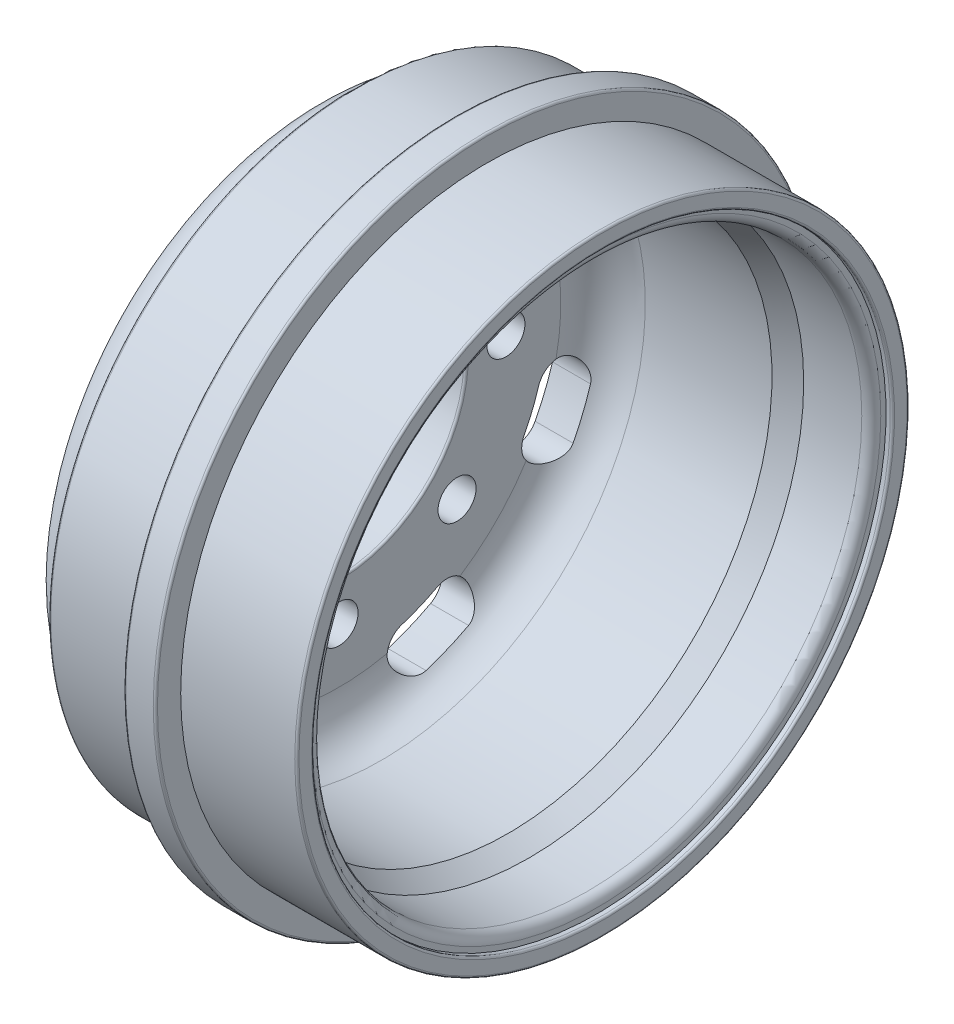
SolidWorks part; units mm, degrees
ref_plane "Plan de face" through (0, 0, 0) normal (0, 0, 1) x (1, 0, 0)
ref_plane "Plan de dessus" through (0, 0, 0) normal (0, 1, 0) x (1, 0, 0)
ref_plane "Plan de droite" through (0, 0, 0) normal (1, 0, 0) x (0, 0, -1)
sketch "Esquisse1" plane through (0, 0, 0) normal (0, 0, 1) x (1, 0, 0)
  line L0 (0, 0) -> (29.5727, 0) construction
  line L1 (0, 6.025) -> (1.75, 6.025)
  line L2 (1.75, 10.5) -> (1.75, 6.025)
  line L3 (14.25, 14.5) -> (8.75, 14.5)
  line L4 (8.75, 14.5) -> (8.75, 15.7)
  line L5 (8.75, 15.7) -> (7.25, 15.7)
  line L6 (7.25, 15.7) -> (7.25, 14.5)
  line L7 (7.25, 14.5) -> (2.5, 14.5)
  line L8 (2.5, 14.5) -> (2.5, 13.5)
  line L9 (0, 6.025) -> (0, 9.75)
  line L10 (0, 9.75) -> (0.5, 9.75)
  line L11 (0.5, 9.75) -> (0.5, 12)
  line L12 (14.25, 14.5) -> (14.25, 13.7)
  line L13 (14.25, 13.7) -> (13.95, 13.7)
  line L14 (13.95, 13.7) -> (13.95, 13.45)
  line L15 (13.5, 13) -> (10.75, 13)
  line L16 (10.75, 13) -> (9.75, 12.5)
  line L17 (9.75, 12.5) -> (3.75, 12.5)
  line L18 (2, 13.5) -> (2.5, 13.5)
  arc A0 (0.5, 12) -> (2, 13.5) centre (2, 12) cw
  arc A1 (13.95, 13.45) -> (13.5, 13) centre (13.5, 13.45) cw
  arc A2 (3.75, 12.5) -> (1.75, 10.5) centre (3.75, 10.5) ccw
  dimension "D1" = 6.025
  dimension "D2" = 9.75
  dimension "D14" = 1.5
  dimension "D22" = 0.45
  dimension "D25" = 10.5
  dimension "D27" = 2
  dimension "D3" = 12
  dimension "D4" = 14.5
  dimension "D5" = 1.5
  dimension "D6" = 5.5
  dimension "D7" = 2.5
  dimension "D8" = 15.7
  dimension "D9" = 14.25
  dimension "D10" = 13.5
  dimension "D11" = 0.5
  dimension "D16" = 10.5
  dimension "D17" = 12.5
  dimension "D18" = 13
  dimension "D19" = 0.8
  dimension "D20" = 0.3
  dimension "D21" = 0.75
  dimension "D23" = 3.5
  dimension "D24" = 1
  dimension "D26" = 1.75
revolve "rev_jante" add sketch "Esquisse1" angle 360 about L0
sketch "Esquisse2" plane through (1.75, 0, 0) normal (1, 0, 0) x (0, 0, -1)
  circle A0 centre (7.9, 0) radius 0.9
  dimension "D1" = 7.9
extrude "trou_moyeu" cut sketch "Esquisse2" against normal through all
pattern_circular "rep_trous_moyeu" count 8 over 360 about axis through (0, 0, 0) along (1, 0, 0) of "trou_moyeu"
sketch "Esquisse4" plane through (0.5, 0, 0) normal (-1, 0, 0) x (0, 0, 1)
  line L0 (0, 0) -> (8.4853, 8.4853) construction
  line L1 (0, 0) -> (0, 12) construction
  line L2 (0, 0) -> (4.5922, 11.0866) construction
  line L3 (0, 0) -> (5.541, 10.6441) construction
  line L4 (0, 0) -> (3.6085, 11.4446) construction
  circle A0 centre (0, 0) radius 12 construction
  arc A3 (5.0215, 9.6462) -> (3.2702, 10.3717) centre (0, 0) ccw
  arc A4 (3.2702, 10.3717) -> (5.1117, 9.5987) centre (0, 0) cw construction
  arc A5 (5.5818, 10.4814) -> (3.5709, 11.3254) centre (0, 0) ccw
  arc A6 (4.6417, 8.7161) -> (2.9695, 9.418) centre (0, 0) ccw
  arc A7 (4.6417, 8.7161) -> (5.5818, 10.4814) centre (5.1117, 9.5987) ccw
  arc A8 (3.5709, 11.3254) -> (2.9695, 9.418) centre (3.2702, 10.3717) ccw
  point P13 (4.2087, 10.0276)
  dimension "D4" = 2
  dimension "D1" = 22.5
  dimension "D2" = 5
  dimension "D3" = 5
extrude "rainure_aeration" cut sketch "Esquisse4" against normal through all
pattern_circular "Répétition circulaire2" count 8 over 360 about axis through (0, 0, 0) along (1, 0, 0) of "rainure_aeration"
fillet "conges" radius 0.1 8 edges at (0, 0, 9.75) (1.75, 0, 6.025) (0.5, 0, 9.75) (2.5, 0, 14.5) (14.25, 0, 13.7) (14.25, 0, 14.5) (7.25, 0, 15.7) (8.75, 0, 15.7)
